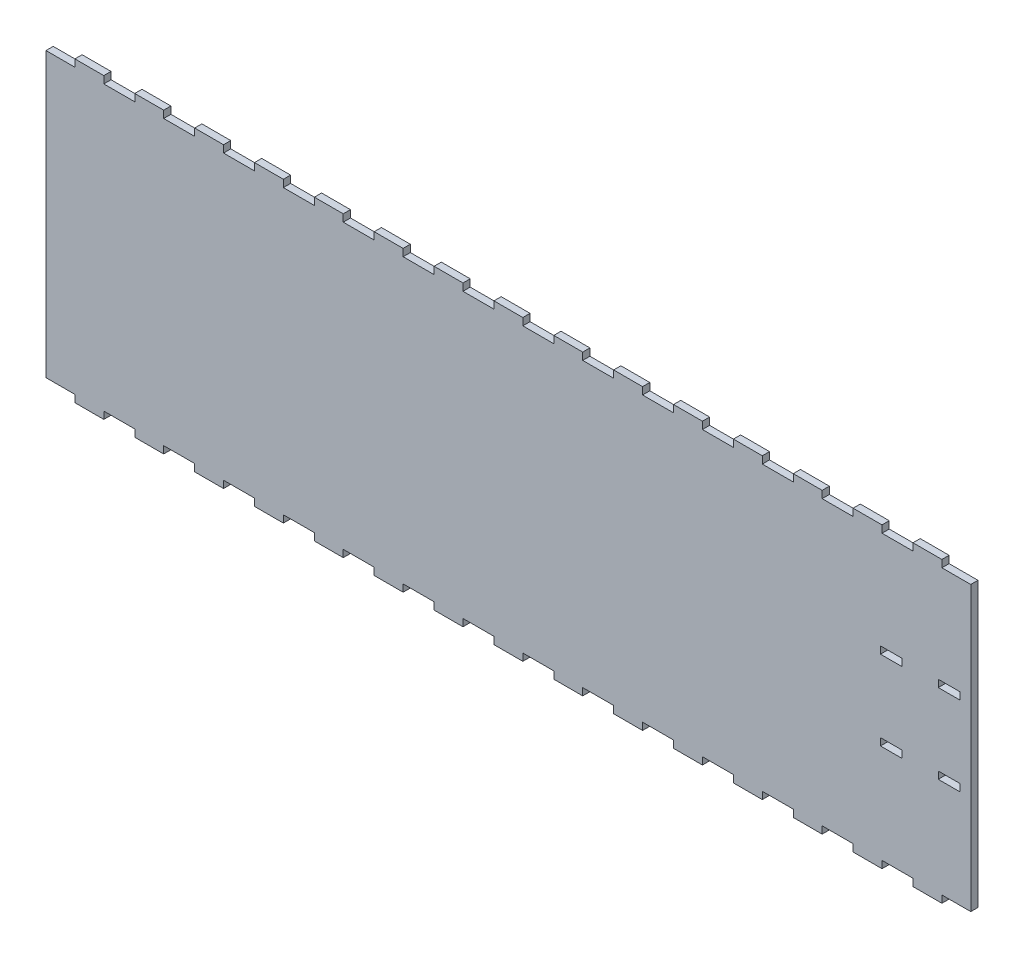
SolidWorks part; units mm, degrees
ref_plane "Front Plane" through (0, 0, 0) normal (0, 0, 1) x (1, 0, 0)
ref_plane "Top Plane" through (0, 0, 0) normal (0, 1, 0) x (1, 0, 0)
ref_plane "Right Plane" through (0, 0, 0) normal (1, 0, 0) x (0, 0, -1)
sketch "Sketch1" plane through (0, 0, 0) normal (0, 0, 1) x (1, 0, 0)
  line L8 (392.1125, 81.3054) -> (392.1125, 78.1304)
  line L9 (401.6375, 81.3054) -> (392.1125, 81.3054)
  line L10 (401.6375, 78.1304) -> (401.6375, 81.3054)
  line L11 (392.1125, 78.1304) -> (401.6375, 78.1304)
  line L16 (392.1125, 46.3804) -> (392.1125, 43.2054)
  line L17 (401.6375, 46.3804) -> (392.1125, 46.3804)
  line L18 (401.6375, 43.2054) -> (401.6375, 46.3804)
  line L19 (392.1125, 43.2054) -> (401.6375, 43.2054)
  line L24 (366.7125, 81.3054) -> (366.7125, 78.1304)
  line L25 (376.2375, 81.3054) -> (366.7125, 81.3054)
  line L26 (376.2375, 78.1304) -> (376.2375, 81.3054)
  line L27 (366.7125, 78.1304) -> (376.2375, 78.1304)
  line L32 (366.7125, 46.3804) -> (366.7125, 43.2054)
  line L33 (376.2375, 46.3804) -> (366.7125, 46.3804)
  line L34 (376.2375, 43.2054) -> (376.2375, 46.3804)
  line L35 (366.7125, 43.2054) -> (376.2375, 43.2054)
  line L280 (406.4, 0) -> (406.4, 124.5108)
  line L281 (406.4, 124.5108) -> (393.7, 124.5108)
  line L282 (393.7, 124.5108) -> (393.7, 127.6858)
  line L283 (393.7, 127.6858) -> (381, 127.6858)
  line L284 (381, 127.6858) -> (381, 124.5108)
  line L285 (381, 124.5108) -> (367.3929, 124.5108)
  line L286 (367.3929, 124.5108) -> (367.3929, 127.6858)
  line L287 (367.3929, 127.6858) -> (354.6929, 127.6858)
  line L288 (354.6929, 127.6858) -> (354.6929, 124.5108)
  line L289 (354.6929, 124.5108) -> (341.0857, 124.5108)
  line L290 (341.0857, 124.5108) -> (341.0857, 127.6858)
  line L291 (341.0857, 127.6858) -> (328.3857, 127.6858)
  line L292 (328.3857, 127.6858) -> (328.3857, 124.5108)
  line L293 (328.3857, 124.5108) -> (314.7786, 124.5108)
  line L294 (314.7786, 124.5108) -> (314.7786, 127.6858)
  line L295 (314.7786, 127.6858) -> (302.0786, 127.6858)
  line L296 (302.0786, 127.6858) -> (302.0786, 124.5108)
  line L297 (302.0786, 124.5108) -> (288.4714, 124.5108)
  line L298 (288.4714, 124.5108) -> (288.4714, 127.6858)
  line L299 (288.4714, 127.6858) -> (275.7714, 127.6858)
  line L300 (275.7714, 127.6858) -> (275.7714, 124.5108)
  line L301 (275.7714, 124.5108) -> (262.1643, 124.5108)
  line L302 (262.1643, 124.5108) -> (262.1643, 127.6858)
  line L303 (262.1643, 127.6858) -> (249.4643, 127.6858)
  line L304 (249.4643, 127.6858) -> (249.4643, 124.5108)
  line L305 (249.4643, 124.5108) -> (235.8571, 124.5108)
  line L306 (235.8571, 124.5108) -> (235.8571, 127.6858)
  line L307 (235.8571, 127.6858) -> (223.1571, 127.6858)
  line L308 (223.1571, 127.6858) -> (223.1571, 124.5108)
  line L309 (223.1571, 124.5108) -> (209.55, 124.5108)
  line L310 (209.55, 124.5108) -> (209.55, 127.6858)
  line L311 (209.55, 127.6858) -> (196.85, 127.6858)
  line L312 (196.85, 127.6858) -> (196.85, 124.5108)
  line L313 (196.85, 124.5108) -> (183.2429, 124.5108)
  line L314 (183.2429, 124.5108) -> (183.2429, 127.6858)
  line L315 (183.2429, 127.6858) -> (170.5429, 127.6858)
  line L316 (170.5429, 127.6858) -> (170.5429, 124.5108)
  line L317 (170.5429, 124.5108) -> (156.9357, 124.5108)
  line L318 (156.9357, 124.5108) -> (156.9357, 127.6858)
  line L319 (156.9357, 127.6858) -> (144.2357, 127.6858)
  line L320 (144.2357, 127.6858) -> (144.2357, 124.5108)
  line L321 (144.2357, 124.5108) -> (130.6286, 124.5108)
  line L322 (130.6286, 124.5108) -> (130.6286, 127.6858)
  line L323 (130.6286, 127.6858) -> (117.9286, 127.6858)
  line L324 (117.9286, 127.6858) -> (117.9286, 124.5108)
  line L325 (117.9286, 124.5108) -> (104.3214, 124.5108)
  line L326 (104.3214, 124.5108) -> (104.3214, 127.6858)
  line L327 (104.3214, 127.6858) -> (91.6214, 127.6858)
  line L328 (91.6214, 127.6858) -> (91.6214, 124.5108)
  line L329 (91.6214, 124.5108) -> (78.0143, 124.5108)
  line L330 (78.0143, 124.5108) -> (78.0143, 127.6858)
  line L331 (78.0143, 127.6858) -> (65.3143, 127.6858)
  line L332 (65.3143, 127.6858) -> (65.3143, 124.5108)
  line L333 (65.3143, 124.5108) -> (51.7071, 124.5108)
  line L334 (51.7071, 124.5108) -> (51.7071, 127.6858)
  line L335 (51.7071, 127.6858) -> (39.0071, 127.6858)
  line L336 (39.0071, 127.6858) -> (39.0071, 124.5108)
  line L337 (39.0071, 124.5108) -> (25.4, 124.5108)
  line L338 (25.4, 124.5108) -> (25.4, 127.6858)
  line L339 (25.4, 127.6858) -> (12.7, 127.6858)
  line L340 (12.7, 127.6858) -> (12.7, 124.5108)
  line L341 (12.7, 124.5108) -> (0, 124.5108)
  line L342 (0, 124.5108) -> (0, 0)
  line L343 (0, 0) -> (12.7, 0)
  line L344 (12.7, 0) -> (12.7, -3.175)
  line L345 (12.7, -3.175) -> (25.4, -3.175)
  line L346 (25.4, -3.175) -> (25.4, 0)
  line L347 (25.4, 0) -> (39.0071, 0)
  line L348 (39.0071, 0) -> (39.0071, -3.175)
  line L349 (39.0071, -3.175) -> (51.7071, -3.175)
  line L350 (51.7071, -3.175) -> (51.7071, 0)
  line L351 (51.7071, 0) -> (65.3143, 0)
  line L352 (65.3143, 0) -> (65.3143, -3.175)
  line L353 (65.3143, -3.175) -> (78.0143, -3.175)
  line L354 (78.0143, -3.175) -> (78.0143, 0)
  line L355 (78.0143, 0) -> (91.6214, 0)
  line L356 (91.6214, 0) -> (91.6214, -3.175)
  line L357 (91.6214, -3.175) -> (104.3214, -3.175)
  line L358 (104.3214, -3.175) -> (104.3214, 0)
  line L359 (104.3214, 0) -> (117.9286, 0)
  line L360 (117.9286, 0) -> (117.9286, -3.175)
  line L361 (117.9286, -3.175) -> (130.6286, -3.175)
  line L362 (130.6286, -3.175) -> (130.6286, 0)
  line L363 (130.6286, 0) -> (144.2357, 0)
  line L364 (144.2357, 0) -> (144.2357, -3.175)
  line L365 (144.2357, -3.175) -> (156.9357, -3.175)
  line L366 (156.9357, -3.175) -> (156.9357, 0)
  line L367 (156.9357, 0) -> (170.5429, 0)
  line L368 (170.5429, 0) -> (170.5429, -3.175)
  line L369 (170.5429, -3.175) -> (183.2429, -3.175)
  line L370 (183.2429, -3.175) -> (183.2429, 0)
  line L371 (183.2429, 0) -> (196.85, 0)
  line L372 (196.85, 0) -> (196.85, -3.175)
  line L373 (196.85, -3.175) -> (209.55, -3.175)
  line L374 (209.55, -3.175) -> (209.55, 0)
  line L375 (209.55, 0) -> (223.1571, 0)
  line L376 (223.1571, 0) -> (223.1571, -3.175)
  line L377 (223.1571, -3.175) -> (235.8571, -3.175)
  line L378 (235.8571, -3.175) -> (235.8571, 0)
  line L379 (235.8571, 0) -> (249.4643, 0)
  line L380 (249.4643, 0) -> (249.4643, -3.175)
  line L381 (249.4643, -3.175) -> (262.1643, -3.175)
  line L382 (262.1643, -3.175) -> (262.1643, 0)
  line L383 (262.1643, 0) -> (275.7714, 0)
  line L384 (275.7714, 0) -> (275.7714, -3.175)
  line L385 (275.7714, -3.175) -> (288.4714, -3.175)
  line L386 (288.4714, -3.175) -> (288.4714, 0)
  line L387 (288.4714, 0) -> (302.0786, 0)
  line L388 (302.0786, 0) -> (302.0786, -3.175)
  line L389 (302.0786, -3.175) -> (314.7786, -3.175)
  line L390 (314.7786, -3.175) -> (314.7786, 0)
  line L391 (314.7786, 0) -> (328.3857, 0)
  line L392 (328.3857, 0) -> (328.3857, -3.175)
  line L393 (328.3857, -3.175) -> (341.0857, -3.175)
  line L394 (341.0857, -3.175) -> (341.0857, 0)
  line L395 (341.0857, 0) -> (354.6929, 0)
  line L396 (354.6929, 0) -> (354.6929, -3.175)
  line L397 (354.6929, -3.175) -> (367.3929, -3.175)
  line L398 (367.3929, -3.175) -> (367.3929, 0)
  line L399 (367.3929, 0) -> (381, 0)
  line L400 (381, 0) -> (381, -3.175)
  line L401 (381, -3.175) -> (393.7, -3.175)
  line L402 (393.7, -3.175) -> (393.7, 0)
  line L403 (393.7, 0) -> (406.4, 0)
extrude "Boss-Extrude1" add sketch "Sketch1" along normal blind 3.175
